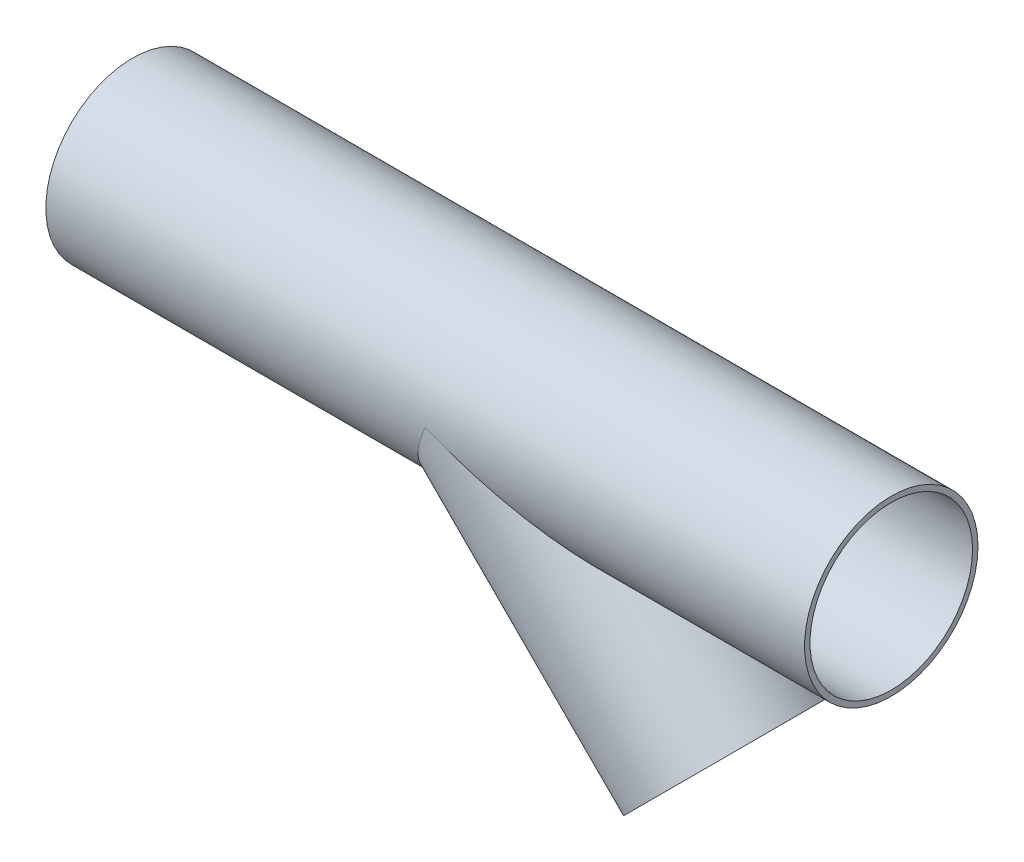
SolidWorks part; units mm, degrees
ref_plane "Plan de face" through (0, 0, 0) normal (0, 0, 1) x (1, 0, 0)
ref_plane "Plan de dessus" through (0, 0, 0) normal (0, 1, 0) x (1, 0, 0)
ref_plane "Plan de droite" through (0, 0, 0) normal (1, 0, 0) x (0, 0, -1)
sketch "Esquisse1" plane through (0, 0, 0) normal (0, 0, 1) x (1, 0, 0)
  line L0 (0, 0) -> (500, 0)
  dimension "D1" = 500
other "Circular tube 114.3 X 3.6(1)"
ref_plane "Plan1" through (0, 0, 0) normal (1, 0, 0) x (0, 1, 0)
sketch "Sketch1" plane through (0, 0, 0) normal (1, 0, 0) x (0, 1, 0)
  circle A0 centre (0, 0) radius 53.55
  circle A1 centre (0, 0) radius 57.15
  point P3 (0, 0)
  dimension "In_dia" = 107.1
  dimension "Out_dia" = 114.3
sketch "Esquisse3" plane through (0, 0, 0) normal (0, 0, 1) x (1, 0, 0)
  line L0 (250, 0) -> (393.5397, -143.5397) construction
  line L1 (0, 0) -> (500, 0) construction
  line L2 (226.3277, -57.15) -> (353.1286, -183.9509)
  line L4 (387.9723, -57.15) -> (433.9509, -103.1286)
  line L5 (209.5888, -40.4112) -> (353.1286, -183.9509) construction
  line L6 (0, -57.15) -> (500, -57.15) construction
  line L7 (290.4112, 40.4112) -> (433.9509, -103.1286) construction
  line L8 (250, 0) -> (226.3277, -57.15)
  line L9 (250, 0) -> (387.9723, -57.15)
  line L10 (433.9509, -103.1286) -> (353.1286, -183.9509)
  dimension "D1" = 202.9958
  dimension "D2" = 45
  dimension "D5" = 114.3
  dimension "D3" = 57.15
  dimension "D4" = 57.15
extrude "Enlèv. mat.-Extru.1" cut sketch "Esquisse3" against normal mid plane 250
sketch "Esquisse4" plane through (0, 0, 0) normal (0, 0, 1) x (1, 0, 0)
  line L0 (250, 0) -> (393.5427, -143.5427)
  line L1 (0, 0) -> (500, 0) construction
  dimension "D1" = 45
  dimension "D2" = 203
ref_plane "Plan2" through (393.5427, -143.5427, 0) normal (0.7071, -0.7071, 0) x (-0.7071, -0.7071, 0)
sketch "Esquisse5" plane through (393.5427, -143.5427, 0) normal (0.7071, -0.7071, 0) x (-0.7071, -0.7071, 0)
  circle A0 centre (0, 0) radius 57.15
  circle A1 centre (0, 0) radius 53.95
  dimension "D1" = 114.3
  dimension "D2" = 3.2
extrude "Boss.-Extru.1" add sketch "Esquisse5" against normal up to next separate body
